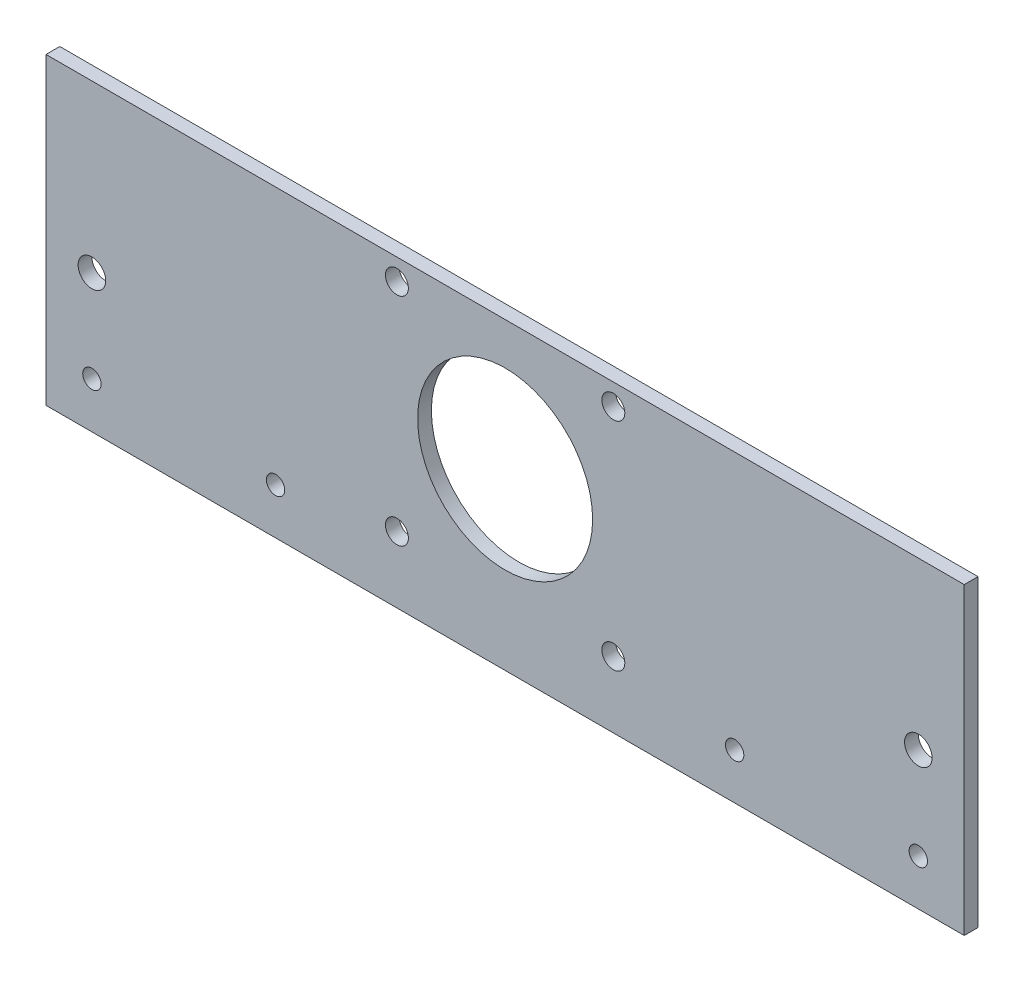
SolidWorks part; units mm, degrees
ref_plane "Ebene vorne" through (0, 0, 0) normal (0, 0, 1) x (1, 0, 0)
ref_plane "Ebene oben" through (0, 0, 0) normal (0, 1, 0) x (1, 0, 0)
ref_plane "Ebene rechts" through (0, 0, 0) normal (1, 0, 0) x (0, 0, -1)
sketch "Skizze1" plane through (0, 0, 0) normal (0, 0, 1) x (1, 0, 0)
  line L1 (0, 0) -> (200, 0)
  line L2 (0, 0) -> (0, 66.2)
  line L3 (0, 66.2) -> (200, 66.2)
  line L4 (200, 0) -> (200, 66.2)
  dimension "D1" = 200
  dimension "D2" = 66.2
extrude "Aufsatz-Linear austragen1" add sketch "Skizze1" along normal blind 3
sketch "Skizze2" plane through (0, 0, 3) normal (0, 0, 1) x (1, 0, 0)
  line L0 (0, 0) -> (200, 0) construction
  line L1 (200, 0) -> (200, 66.2) construction
  circle A0 centre (100, 38) radius 19.0625
  dimension "D1" = 38.125
  dimension "D3" = 100
  dimension "D2" = 38
extrude "Schnitt-Linear austragen1" cut sketch "Skizze2" against normal blind 24
sketch "Skizze3" plane through (0, 0, 0) normal (0, 0, -1) x (-1, 0, 0)
  line L0 (-200, 0) -> (-200, 66.2) construction
  line L1 (0, 0) -> (-200, 0) construction
  line L2 (0, 66.2) -> (0, 0) construction
  circle A0 centre (-190, 10) radius 2
  circle A1 centre (-150, 10) radius 2
  circle A4 centre (-50, 10) radius 2
  circle A5 centre (-10, 10) radius 2
  dimension "D1" = 4
  dimension "D2" = 10
  dimension "D3" = 10
  dimension "D4" = 10
  dimension "D5" = 50
  dimension "D6" = 50
extrude "Schnitt-Linear austragen2" cut sketch "Skizze3" against normal blind 10
sketch "Skizze4" plane through (0, 0, 0) normal (0, 0, -1) x (-1, 0, 0)
  line L0 (0, 66.2) -> (0, 0) construction
  line L1 (-200, 0) -> (-200, 66.2) construction
  line L2 (0, 0) -> (-200, 0) construction
  circle A0 centre (-190, 30) radius 3
  circle A1 centre (-10, 30) radius 3
  dimension "D3" = 6
  dimension "D1" = 10
  dimension "D2" = 10
  dimension "D4" = 30
extrude "Schnitt-Linear austragen3" cut sketch "Skizze4" against normal blind 10
sketch "Skizze5" plane through (0, 0, 0) normal (0, 0, -1) x (-1, 0, 0)
  line L0 (0, 66.2) -> (0, 0) construction
  line L1 (-200, 66.2) -> (0, 66.2) construction
  circle A0 centre (-76.43, 61.57) radius 2.5
  circle A1 centre (-123.57, 61.57) radius 2.5
  circle A2 centre (-123.57, 14.43) radius 2.5
  circle A3 centre (-76.43, 14.43) radius 2.5
  dimension "D1" = 5
  dimension "D2" = 76.43
  dimension "D3" = 47.14
  dimension "D4" = 4.63
  dimension "D5" = 47.14
extrude "Schnitt-Linear austragen4" cut sketch "Skizze5" against normal blind 10
